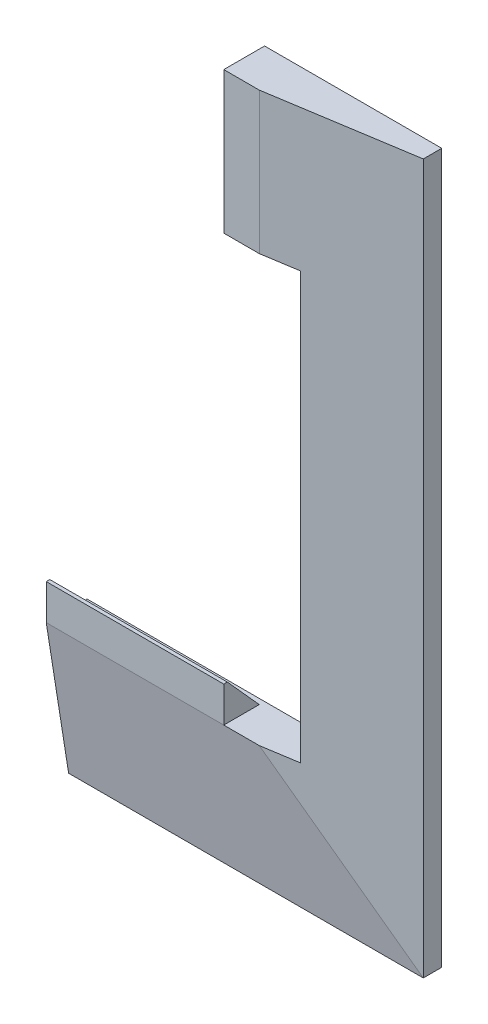
SolidWorks part; units mm, degrees
ref_plane "Płaszczyzna przednia" through (0, 0, 0) normal (0, 0, 1) x (1, 0, 0)
ref_plane "Płaszczyzna górna" through (0, 0, 0) normal (0, 1, 0) x (1, 0, 0)
ref_plane "Płaszczyzna prawa" through (0, 0, 0) normal (1, 0, 0) x (0, 0, -1)
sketch "Szkic2" plane through (0, 0, 0) normal (0, 0, 1) x (1, 0, 0)
  line L0 (18.5428, 83.2454) -> (18.5428, 43.3454)
  line L1 (-81.3572, 83.2454) -> (18.5428, 83.2454)
  line L2 (-81.3572, 83.2454) -> (-81.3572, -116.5546)
  line L3 (-81.3572, -116.5546) -> (18.5428, -116.5546)
  line L5 (-51.4572, 43.3454) -> (18.5428, 43.3454)
  line L6 (-51.4572, 43.3454) -> (-51.4572, -76.6546)
  line L7 (-51.4572, -76.6546) -> (18.5428, -76.6546)
  line L9 (-51.4572, -16.6546) -> (-81.3572, -16.6546) construction
  line L10 (18.5428, 43.3454) -> (18.5428, 83.2454) construction
  line L11 (18.5428, -76.6546) -> (18.5428, -116.5546) construction
  line L12 (18.5428, -76.6546) -> (18.5428, -116.5546)
  dimension "D1" = 199.8
  dimension "D3" = 120
  dimension "D4" = 29.9
extrude "Dodanie-wyciągnięcie1" add sketch "Szkic2" along normal blind 5.2
ref_plane "Płaszczyzna1" through (0, 0, 11.5) normal (0, 0, 1) x (1, 0, 0)
sketch "Szkic3" plane through (0, 0, 11.5) normal (0, 0, 1) x (1, 0, 0)
  line L5 (18.5428, -76.6546) -> (-51.4572, -76.6546) construction
  line L6 (-41.4572, -76.6546) -> (18.5428, -76.6546)
  line L12 (-41.4572, -76.6546) -> (-41.4572, 83.2454)
  line L13 (18.5428, 83.2454) -> (-81.3572, 83.2454) construction
  line L14 (-41.4572, 83.2454) -> (18.5428, 83.2454)
  line L15 (18.5428, 83.2454) -> (18.5428, -76.6546)
sketch "Szkic5" plane through (0, 0, 5.2) normal (0, 0, 1) x (1, 0, 0)
  line L1 (-81.3572, 83.2454) -> (18.5428, 83.2454)
  line L2 (-81.3572, 83.2454) -> (-81.3572, -116.5546)
  line L3 (-81.3572, -116.5546) -> (18.5428, -116.5546)
  line L4 (18.5428, 83.2454) -> (18.5428, -116.5546)
loft "Wyciągnięcie po profilach3" add profiles "Szkic3", "Szkic5"
sketch "Szkic6" plane through (-51.4572, 0, 0) normal (1, 0, 0) x (0, 0, -1)
  line L1 (0, 43.3454) -> (-49.2712, 43.3454)
  line L2 (0, 43.3454) -> (0, -76.6546)
  line L3 (0, -76.6546) -> (-49.2712, -76.6546)
  line L4 (-49.2712, 43.3454) -> (-49.2712, -76.6546)
extrude "Wytnij-wyciągnięcie1" cut sketch "Szkic6" along normal blind 78
sketch "Szkic7" plane through (-51.4572, 0, 0) normal (1, 0, 0) x (0, 0, -1)
  line L0 (-5.12, -76.6546) -> (-5.12, -36.5546) construction
  line L2 (-5.12, -36.5546) -> (-5.12, 3.2454) construction
  line L3 (-5.12, 3.2454) -> (-5.12, 43.3454) construction
  line L5 (0, -76.6546) -> (0, 43.3454) construction
  line L7 (-5.12, -34.1298) -> (-7.22, -35.3422)
  line L8 (-7.22, -35.3422) -> (-7.22, -37.7671)
  line L9 (-7.22, -37.7671) -> (-5.12, -38.9795)
  line L10 (-5.12, -38.9795) -> (-3.02, -37.7671)
  line L11 (-3.02, -37.7671) -> (-3.02, -35.3422)
  line L12 (-3.02, -35.3422) -> (-5.12, -34.1298)
  line L13 (-5.12, 5.6702) -> (-7.22, 4.4578)
  line L14 (-7.22, 4.4578) -> (-7.22, 2.0329)
  line L15 (-7.22, 2.0329) -> (-5.12, 0.8205)
  line L16 (-5.12, 0.8205) -> (-3.02, 2.0329)
  line L17 (-3.02, 2.0329) -> (-3.02, 4.4578)
  line L18 (-3.02, 4.4578) -> (-5.12, 5.6702)
  circle A0 centre (-5.12, -36.5546) radius 2.1 construction
  circle A1 centre (-5.12, 3.2454) radius 2.1 construction
  dimension "D2" = 4.2
  dimension "D3" = 4.2
  dimension "D1" = 5.12
extrude "Wytnij-wyciągnięcie2" cut sketch "Szkic7" against normal blind 5.6
sketch "Szkic9" plane through (-51.4572, 0, 0) normal (1, 0, 0) x (0, 0, -1)
  circle A0 centre (-5.12, 3.2454) radius 2.4249
  circle A1 centre (-5.12, -36.5546) radius 2.4249
  circle A2 centre (-5.12, 3.2454) radius 1.2
  circle A3 centre (-5.12, -36.5546) radius 1.2
extrude "Dodanie-wyciągnięcie3" add sketch "Szkic9" against normal blind 3.8
sketch "Szkic10" plane through (0, 0, 11.5) normal (0, 0, 1) x (1, 0, 0)
  line L0 (-41.4572, 83.2454) -> (-41.4572, 43.3454) construction
  line L1 (-31.4572, 83.2454) -> (18.5428, 83.2454)
  line L2 (-31.4572, 83.2454) -> (-31.4572, 43.3454)
  line L3 (-31.4572, 43.3454) -> (18.5428, 43.3454)
  line L4 (18.5428, 83.2454) -> (18.5428, 43.3454)
  dimension "D1" = 10
extrude "Wytnij-wyciągnięcie4" cut sketch "Szkic10" against normal blind 24
mirror "Lustro1" about plane through (18.5428, 83.2454, 5.2) normal (-1, 0, 0) of bodies 128
move or copy body "Obiekt-Przenieś/Kopiuj1" bodies to move or copy 129 copy no translate (34.8901, 0, 0) parameters "D1"=34.8901, "D2"=0, "D3"=0
delete or keep bodies "Obiekt-Usuń/zachowaj 1" type delete bodies bodies 128
sketch "Szkic11" plane through (53.433, 0, 0) normal (-1, 0, 0) x (0, 0, 1)
  line L0 (11.5, -76.6546) -> (1.5, -76.6546)
  line L1 (9.9211, -76.6546) -> (0, -76.6546) construction
  line L2 (1.5, -76.6546) -> (10.5, -66.6546)
  line L3 (10.5, -66.6546) -> (11.5, -66.6546)
  line L4 (11.5, -66.6546) -> (11.5, -76.6546)
  point P3 (0, 0)
  point P4 (6.6376, -76.6546)
  point P9 (0, 0)
  point P10 (8.9645, -66.6929)
extrude "Dodanie-wyciągnięcie4" add sketch "Szkic11" against normal blind 50
